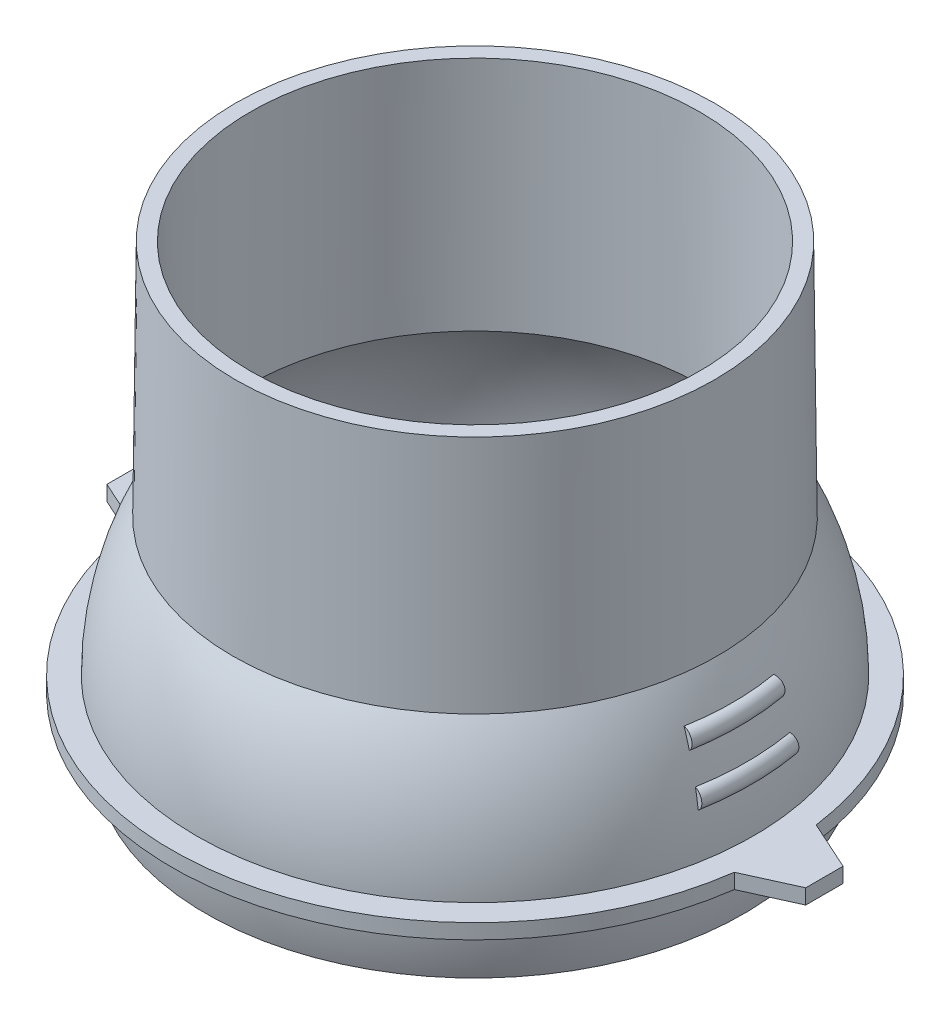
SolidWorks part; units mm, degrees
material "ABS"
ref_plane "Front Plane" through (0, 0, 0) normal (0, 0, 1) x (1, 0, 0)
ref_plane "Top Plane" through (0, 0, 0) normal (0, 1, 0) x (1, 0, 0)
ref_plane "Right Plane" through (0, 0, 0) normal (1, 0, 0) x (0, 0, -1)
sketch "REFERENCE" plane through (0, 0, 0) normal (1, 0, 0) x (0, 0, -1)
  line L0 (0, 0) -> (45, 0) construction
  line L1 (0, 50.3555) -> (0, -50.3555) construction
  line L2 (45, 50.3555) -> (45, -50.3555) construction
  line L3 (45, 0) -> (42.5, -47.7028) construction
  line L4 (40, -105) -> (42.1213, -107.1213) construction
  line L5 (42.5, -47.7028) -> (45.5, -47.7028) construction
  line L6 (45, 0) -> (48, 0) construction
  line L7 (48, 0) -> (45.5, -47.7028) construction
  arc A0 (42.5, -47.7028) -> (40, -105) centre (6.6031, -74.8397) cw construction
  arc A1 (45.5, -47.7028) -> (42.1213, -107.1213) centre (10.1085, -75.4957) cw construction
  point P5 (0, 0)
  point P8 (45, 0)
  point P9 (45, 0)
  dimension "D2" = 45
  dimension "D6" = 45
  dimension "D1" = 45
  dimension "D3" = 3
  dimension "D4" = 105
  dimension "D5" = 3
sketch "Sketch2" plane through (0, 0, 0) normal (1, 0, 0) x (0, 0, -1)
  line L0 (42.1213, -107.1213) -> (44.2426, -109.2426) construction
  line L1 (0, 50.3555) -> (0, -50.3555) construction
  line L2 (40, -105) -> (42.1213, -107.1213) construction
  line L3 (45.5, -47.7028) -> (48.5, -47.7028) construction
  line L4 (45.5, -47.7028) -> (45, 0)
  line L5 (45, 50.3555) -> (45, -50.3555) construction
  line L6 (45, 0) -> (48, 0)
  line L7 (48, 0) -> (48.5, -47.7028)
  line L8 (51.126, -88.9639) -> (53.8837, -89.7028)
  arc A2 (45.5, -47.7028) -> (42.1213, -107.1213) centre (0, -74.9209) cw construction
  arc A3 (48.5, -47.7028) -> (44.2426, -109.2426) centre (0, -75.2647) cw construction
  arc A4 (45.5, -47.7028) -> (51.126, -88.9639) centre (0, -74.9209) cw
  arc A5 (48.5, -47.7028) -> (53.8837, -89.7028) centre (0, -75.2647) cw
  dimension "D2" = 30
  dimension "D1" = 3
revolve "Revolve1" add sketch "Sketch2" angle 360 about L1
ref_axis "Axis1" through (0, -123.2095, 0) along (0, 1, 0)
sketch "Sketch3" plane through (0, 0, 0) normal (1, 0, 0) x (0, 0, -1)
  line L0 (55.7845, -75.2647) -> (60.7038, -75.2647)
  line L1 (60.7038, -75.2647) -> (60.7038, -78.2647)
  line L2 (60.7038, -78.2647) -> (55.7038, -78.2647)
  line L4 (48.5, -47.7028) -> (48, 0)
  line L5 (48, 0) -> (45, 0)
  line L6 (45, 0) -> (45.5, -47.7028)
  line L7 (51.126, -88.9639) -> (53.8837, -89.7028)
  line L8 (48.5, -47.7028) -> (48, 0) construction
  line L9 (48, 0) -> (45, 0) construction
  line L10 (45, 0) -> (45.5, -47.7028) construction
  line L11 (51.126, -88.9639) -> (53.8837, -89.7028) construction
  arc A0 (55.7038, -78.2647) -> (55.7845, -75.2647) centre (0, -75.2647) ccw
  arc A2 (53.8837, -89.7028) -> (48.5, -47.7028) centre (0, -75.2647) ccw
  arc A3 (51.126, -88.9639) -> (45.5, -47.7028) centre (0, -74.9209) ccw
  arc A4 (53.8837, -89.7028) -> (48.5, -47.7028) centre (0, -75.2647) ccw construction
  arc A5 (51.126, -88.9639) -> (45.5, -47.7028) centre (0, -74.9209) ccw construction
  dimension "D2" = 3
  dimension "D3" = 5
  dimension "D1" = 0
revolve "Revolve2" add sketch "Sketch3" angle 360 about axis through (0, -123.2095, 0) along (0, 1, 0)
sketch "Sketch4" plane through (0, -75.2647, 0) normal (0, 1, 0) x (1, 0, 0)
  line L0 (-97.9028, 0) -> (97.9028, 0) construction
  line L1 (70, 3.7436) -> (70, -3.7436)
  line L2 (70, 3.7436) -> (60.147, 8.2029)
  line L3 (70, -3.7436) -> (60.147, -8.2029)
  line L4 (0, 0) -> (0, 26.2618) construction
  line L5 (-70, -3.7436) -> (-60.147, -8.2029)
  line L6 (-70, 3.7436) -> (-70, -3.7436)
  line L7 (-70, 3.7436) -> (-60.147, 8.2029)
  circle A0 centre (0, 0) radius 60.7038 construction
  arc A1 (60.147, 8.2029) -> (60.147, -8.2029) centre (0, 0) cw
  arc A2 (-60.147, 8.2029) -> (-60.147, -8.2029) centre (0, 0) ccw
  point P4 (0, 0)
  point P8 (70, 0)
  dimension "D1" = 70
  dimension "D2" = 114.351
extrude "Boss-Extrude1" add sketch "Sketch4" against normal blind 3
sketch "Sketch5" plane through (0, 0, 0) normal (0, 0, 1) x (1, 0, 0)
  arc A0 (51.6418, -54.169) -> (52.935, -57.6639) centre (51.6067, -56.1687) cw
  arc A1 (55.7845, -75.2647) -> (48.5, -47.7028) centre (0, -75.2647) ccw construction
  arc A2 (54.442, -63.1) -> (55.1264, -66.7214) centre (54.0203, -65.0551) cw
  arc A3 (51.6418, -54.169) -> (52.935, -57.6639) centre (0, -75.2647) cw
  arc A4 (54.442, -63.1) -> (55.1264, -66.7214) centre (0, -75.2647) cw
  dimension "D1" = 2
  dimension "D2" = 2
revolve "Revolve3" add sketch "Sketch5" angle 20 mid plane about axis through (0, -123.2095, 0) along (0, 1, 0)
mirror "Mirror1" about plane through (0, 0, 0) normal (1, 0, 0) of "Revolve3"
